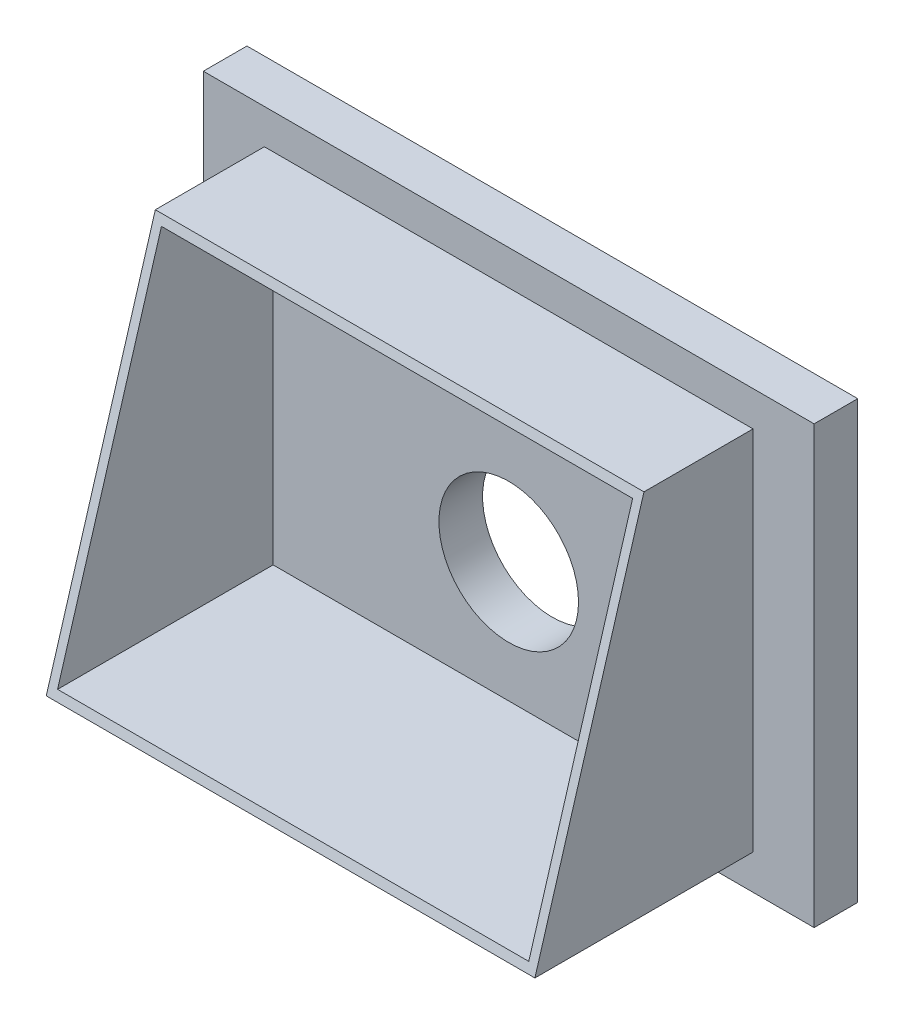
SolidWorks part; units mm, degrees
ref_plane "Front Plane" through (0, 0, 0) normal (0, 0, 1) x (1, 0, 0)
ref_plane "Top Plane" through (0, 0, 0) normal (0, 1, 0) x (1, 0, 0)
ref_plane "Right Plane" through (0, 0, 0) normal (1, 0, 0) x (0, 0, -1)
sketch "Sketch1" plane through (0, 0, 0) normal (0, 0, 1) x (1, 0, 0)
  line L1 (-350, 250) -> (350, 250)
  line L2 (-350, 250) -> (-350, -250)
  line L3 (-350, -250) -> (350, -250)
  line L4 (350, 250) -> (350, -250)
  line L5 (-350, 250) -> (350, -250) construction
  line L6 (-350, -250) -> (350, 250) construction
  point P0 (0, 0)
  dimension "D1" = 500
  dimension "D2" = 700
extrude "Boss-Extrude1" add sketch "Sketch1" along normal blind 50
sketch "Sketch2" plane through (0, 0, 50) normal (0, 0, 1) x (1, 0, 0)
  line L1 (-270, 200) -> (270, 200)
  line L2 (-270, 200) -> (-270, -200)
  line L3 (-270, -200) -> (270, -200)
  line L4 (270, 200) -> (270, -200)
  line L5 (-270, 200) -> (270, -200) construction
  line L6 (-270, -200) -> (270, 200) construction
  point P0 (0, 0)
  dimension "D1" = 400
  dimension "D2" = 540
extrude "Extrude-Thin1" add sketch "Sketch2" along normal blind 250 thin thin type one direction wall 10
sketch "Sketch3" plane through (-280, 0, 0) normal (-1, 0, 0) x (0, 0, 1)
  line L0 (175, 210) -> (300, -210)
  line L1 (300, 210) -> (50, 210) construction
  line L2 (175, 210) -> (300, 210)
  line M5 (300, -210) -> (300, 210)
  line M6 (300, 210) -> (50, 210)
  dimension "D1" = 125
extrude "Cut-Extrude5" cut sketch "Sketch3" against normal through all and the other way through all contours L0 M6 M5
sketch "Sketch4" plane through (0, 0, 50) normal (0, 0, 1) x (1, 0, 0)
  line L0 (-350, -250) -> (350, -250) construction
  circle A0 centre (0, -62) radius 80
  point P5 (0, -250)
  dimension "D1" = 160
  dimension "188" = 188
extrude "Cut-Extrude6" cut sketch "Sketch4" against normal through all
